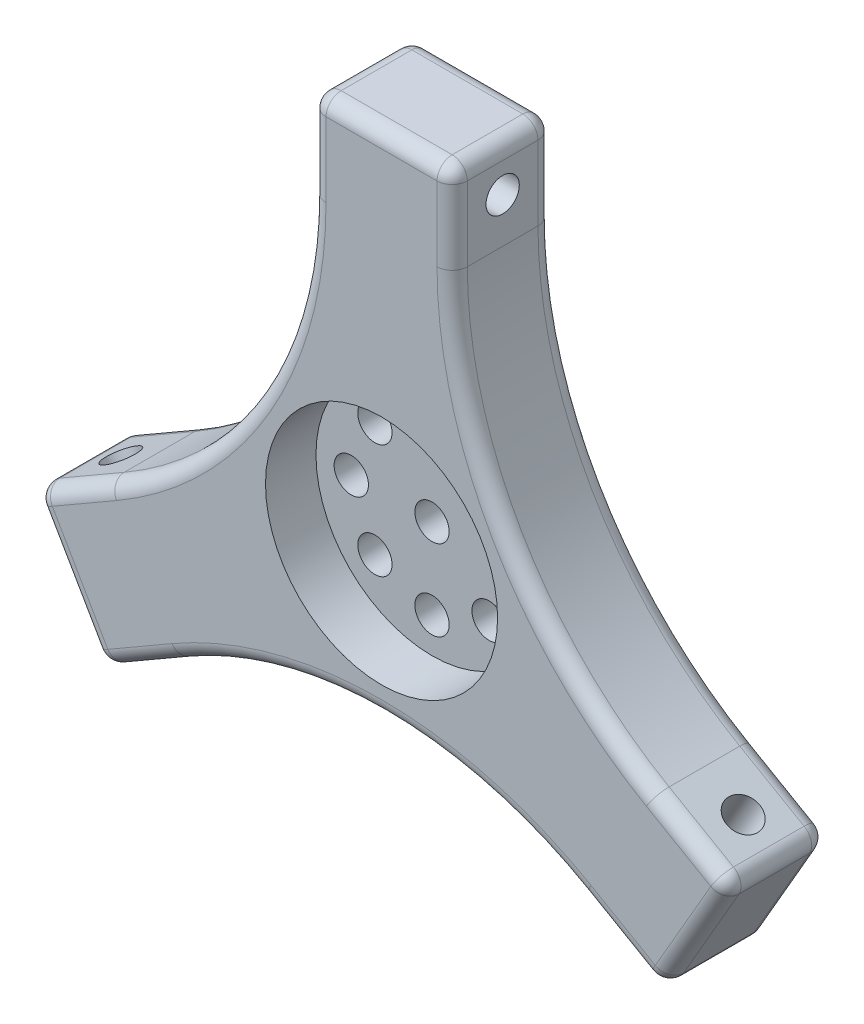
SolidWorks part; units mm, degrees
ref_plane "Front Plane" through (0, 0, 0) normal (0, 0, 1) x (1, 0, 0)
ref_plane "Top Plane" through (0, 0, 0) normal (0, 1, 0) x (1, 0, 0)
ref_plane "Right Plane" through (0, 0, 0) normal (1, 0, 0) x (0, 0, -1)
sketch "Sketch1" plane through (0, 0, 0) normal (0, 0, 1) x (1, 0, 0)
  line L0 (0, 0) -> (0, 36) construction
  line L2 (7, 36) -> (-7, 36)
  line L3 (7, 36) -> (7, 4.0415)
  line L5 (-7, 36) -> (-7, 4.0415)
  line L7 (34.6769, -11.9378) -> (7, 4.0415)
  line L8 (0, 0) -> (31.1769, -18) construction
  line L9 (27.6769, -24.0622) -> (0, -8.0829)
  line L10 (27.6769, -24.0622) -> (34.6769, -11.9378)
  line L11 (-27.6769, -24.0622) -> (0, -8.0829)
  line L12 (0, 0) -> (-31.1769, -18) construction
  line L13 (-34.6769, -11.9378) -> (-7, 4.0415)
  line L14 (-34.6769, -11.9378) -> (-27.6769, -24.0622)
  point P4 (0, 36)
  dimension "D1" = 36
  dimension "D2" = 14
  dimension "D3" = 3
extrude "Boss-Extrude1" add sketch "Sketch1" along normal blind 10
fillet "Fillet1" radius 40 3 edges at (0, -8.0829, 5) (7, 4.0415, 5) (-7, 4.0415, 5)
hole_wizard "M4x0.7 Tapped Hole1" positions "Sketch18" profile "Sketch19" tap size "M4x0.7" standard "ANSI Metric" end condition up to next
sketch "Sketch18" plane through (-7, 0, 0) normal (-1, 0, 0) x (0, 0, 1)
  line L0 (5, 36) -> (5, 27.1355) construction
  line L1 (10, 36) -> (0, 36) construction
  line L2 (0, 27.1355) -> (10, 27.1355) construction
  point P0 (5, 31.5677)
sketch "Sketch19" plane through (-7, 31.5677, 5) normal (0, 1, 0) x (0, 0, 1)
  line L0 (0, 0) -> (0, 17.8398)
  line L1 (0, 17.8398) -> (1.65, 17.8398)
  line L2 (1.65, 17.8398) -> (1.65, 0)
  line L5 (1.65, 0) -> (0, 0)
  line L11 (0, -6.35) -> (0, 107.95) construction
  dimension "Thru Tap Drill Dia." = 3.3
  dimension "Thru Tap Drill Depth" = 17.8398
cosmetic thread "Hole Thread5" parameters "D2"=4
hole_wizard "M3 Clearance Hole3" positions "Sketch21" profile "Sketch22" hole size "M3" standard "ANSI Metric" end condition up to next
sketch "Sketch21" plane through (0, 0, 10) normal (0, 0, 1) x (1, 0, 0)
  point P0 (0, 0)
  point P3 (0, 8)
  point P11 (5.6569, 5.6569)
  point P12 (8, 0)
  point P13 (5.6569, -5.6569)
  point P14 (0, -8)
  point P15 (-5.6569, -5.6569)
  point P16 (-8, 0)
  point P17 (-5.6569, 5.6569)
  dimension "D1" = 8
sketch "Sketch22" plane through (0, 0, 10) normal (1, 0, 0) x (0, -1, 0)
  line L0 (0, 0) -> (0, 10)
  line L1 (0, 10) -> (1.7, 10)
  line L2 (1.7, 10) -> (1.7, 0)
  line L5 (1.7, 0) -> (0, 0)
  line L11 (0, -6.35) -> (0, 107.95) construction
  dimension "Thru Hole Dia." = 3.4
  dimension "Thru Hole Depth" = 10
sketch "Sketch23" plane through (0, 0, 10) normal (0, 0, 1) x (1, 0, 0)
  circle A0 centre (0, 0) radius 11.5
extrude "Cut-Extrude3" cut sketch "Sketch23" against normal blind 5
pattern_circular "CirPattern2" count 3 every 120 about axis through (0, 0, 5) along (0, 0, 1) of "M4x0.7 Tapped Hole1"
cosmetic thread "Hole Thread6" parameters "D2"=4
cosmetic thread "Hole Thread7" parameters "D2"=4
fillet "Fillet2" radius 1.5 30 edges at (-7, 31.5677, 10) (-30.8385, -9.7217, 10) (30.8385, -9.7217, 10) (7, 31.5677, 10) (-23.8385, -21.846, 10) (23.8385, -21.846, 10) (23.8385, -21.846, 0) (-23.8385, -21.846, 0) (-30.8385, -9.7217, 0) (-7, 31.5677, 0) (7, 31.5677, 0) (30.8385, -9.7217, 0) (-12.359, 7.1355, 10) (12.359, 7.1355, 10) (0, -14.2709, 10) (0, -14.2709, 0) (-12.359, 7.1355, 0) (12.359, 7.1355, 0) (34.6769, -11.9378, 5) (27.6769, -24.0622, 5) (-27.6769, -24.0622, 5) (-34.6769, -11.9378, 5) (7, 36, 5) (-7, 36, 5) (0, 36, 0) (0, 36, 10) (-31.1769, -18, 0) (-31.1769, -18, 10) (31.1769, -18, 0) (31.1769, -18, 10)
